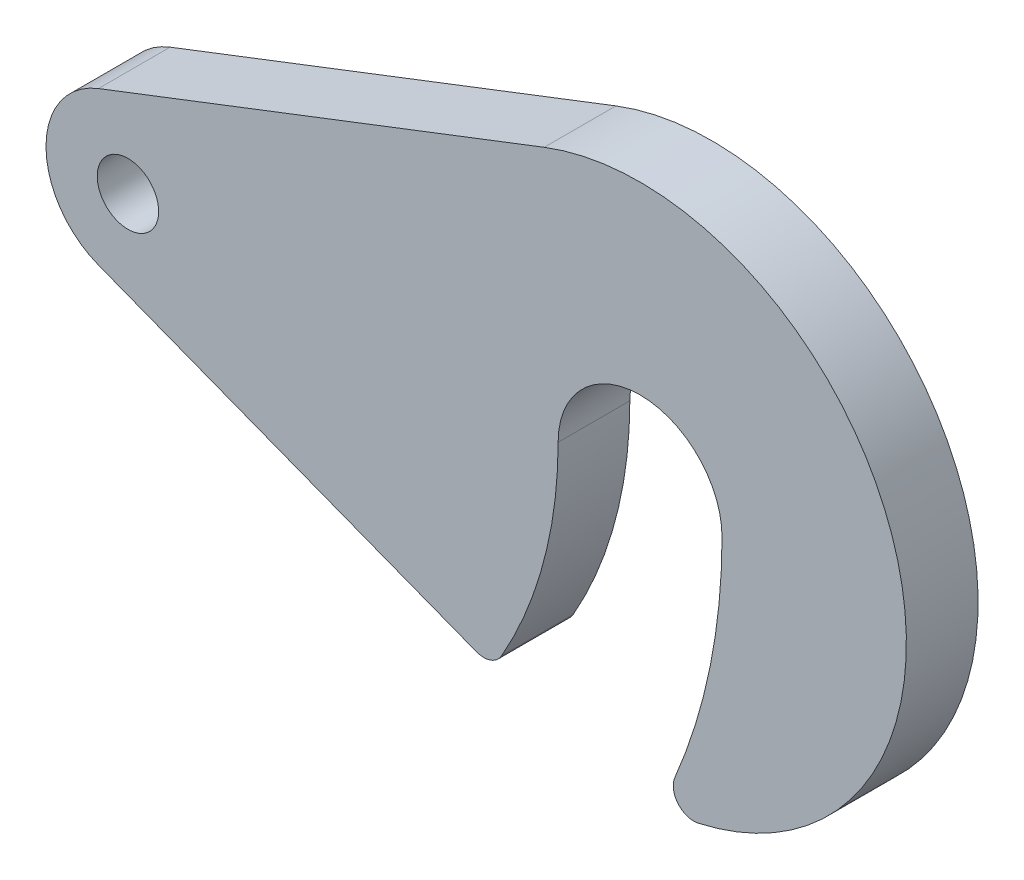
SolidWorks part; units mm, degrees
ref_plane "Přední rovina" through (0, 0, 0) normal (0, 0, 1) x (1, 0, 0)
ref_plane "Horní rovina" through (0, 0, 0) normal (0, 1, 0) x (1, 0, 0)
ref_plane "Pravá rovina" through (0, 0, 0) normal (1, 0, 0) x (0, 0, -1)
sketch "Skica1" plane through (0, 0, 0) normal (0, 0, 1) x (1, 0, 0)
  line L0 (40.64, 24.2568) -> (-2.88, 7.4636)
  line L1 (-2.88, -7.4636) -> (34.0159, -21.7007)
  line L2 (-11.2884, 0) -> (78.8628, 0) construction
  line L3 (0, 16.9331) -> (0, -20.0289) construction
  line L4 (50, 32.2588) -> (50, 0) construction
  arc A0 (-2.88, 7.4636) -> (-2.88, -7.4636) centre (0, 0) ccw
  circle A1 centre (0, 0) radius 3
  arc A2 (53.3987, -22.6403) -> (55.6767, -25.3727) centre (55.24, -23.421) ccw
  arc A3 (58, 0) -> (42, 0) centre (50, 0) ccw
  arc A4 (38.61, -31.7689) -> (50, 0) centre (0, 0) ccw construction
  arc A5 (36.4727, -20.8265) -> (42, 0) centre (0, 0) ccw
  arc A6 (36.4727, -20.8265) -> (34.0159, -21.7007) centre (34.7359, -19.8348) cw
  arc A7 (53.3987, -22.6403) -> (58, 0) centre (0, 0) ccw
  arc A8 (55.6767, -25.3727) -> (40.64, 24.2568) centre (50, 0) ccw
  dimension "D1" = 6
  dimension "D2" = 8
  dimension "D3" = 8
  dimension "D4" = 26
  dimension "D6" = 2
  dimension "D5" = 50
extrude "Přidat vysunutím2" add sketch "Skica1" along normal blind 7
